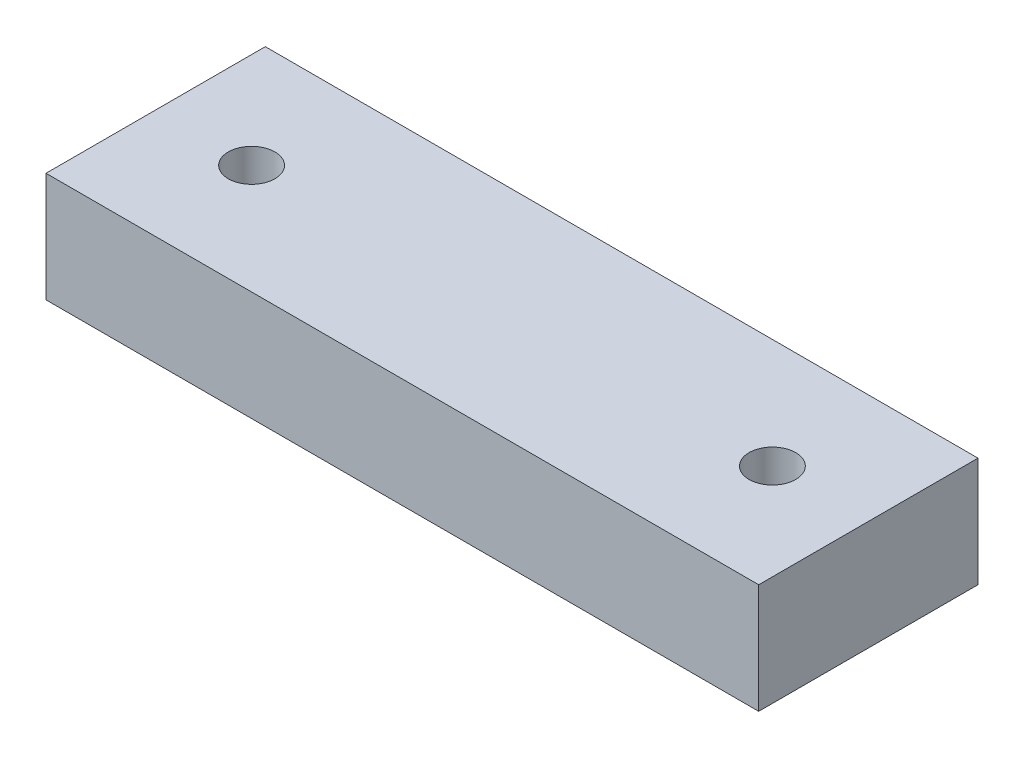
SolidWorks part; units mm, degrees
ref_plane "前视基准面" through (0, 0, 0) normal (0, 0, 1) x (1, 0, 0)
ref_plane "上视基准面" through (0, 0, 0) normal (0, 1, 0) x (1, 0, 0)
ref_plane "右视基准面" through (0, 0, 0) normal (1, 0, 0) x (0, 0, -1)
sketch "草图1" plane through (0, 0, 0) normal (0, 1, 0) x (1, 0, 0)
  line L1 (-65, 20) -> (65, 20)
  line L2 (-65, 20) -> (-65, -20)
  line L3 (-65, -20) -> (65, -20)
  line L4 (65, 20) -> (65, -20)
  line L5 (-65, 20) -> (65, -20) construction
  line L6 (-65, -20) -> (65, 20) construction
  point P0 (0, 0)
  dimension "D1" = 130
  dimension "D2" = 40
extrude "凸台-拉伸1" add sketch "草图1" along normal blind 20
sketch "草图2" plane through (0, 20, 0) normal (0, 1, 0) x (1, 0, 0)
  line L0 (47.5, 0) -> (-47.5, 0) construction
  line L2 (0, 36.4384) -> (0, -29.528) construction
  dimension "D1" = 95
hole_wizard "M10 螺纹孔1" positions "草图4" profile "草图5" tap size "M10" standard "GB"
sketch "草图4" plane through (0, 20, 0) normal (0, 1, 0) x (1, 0, 0)
  point P1 (47.5, 0)
  point P4 (-47.5, 0)
sketch "草图5" plane through (47.5, 20, 0) normal (1, 0, 0) x (0, 0, 1)
  line L0 (0, 0) -> (0, 27.0537)
  line L1 (0, 27.0537) -> (4.25, 24.5)
  line L2 (4.25, 24.5) -> (4.25, 0)
  line L5 (4.25, 0) -> (0, 0)
  line L10 (0, 27.0537) -> (-4.25, 24.5) construction
  line L11 (0, -6.35) -> (0, 107.95) construction
  dimension "螺纹孔钻头直径" = 8.5
  dimension "螺纹孔钻头深度" = 24.5
  dimension "导头角度" = 118
cosmetic thread "孔螺蚊线1"
cosmetic thread "孔螺蚊线2"
